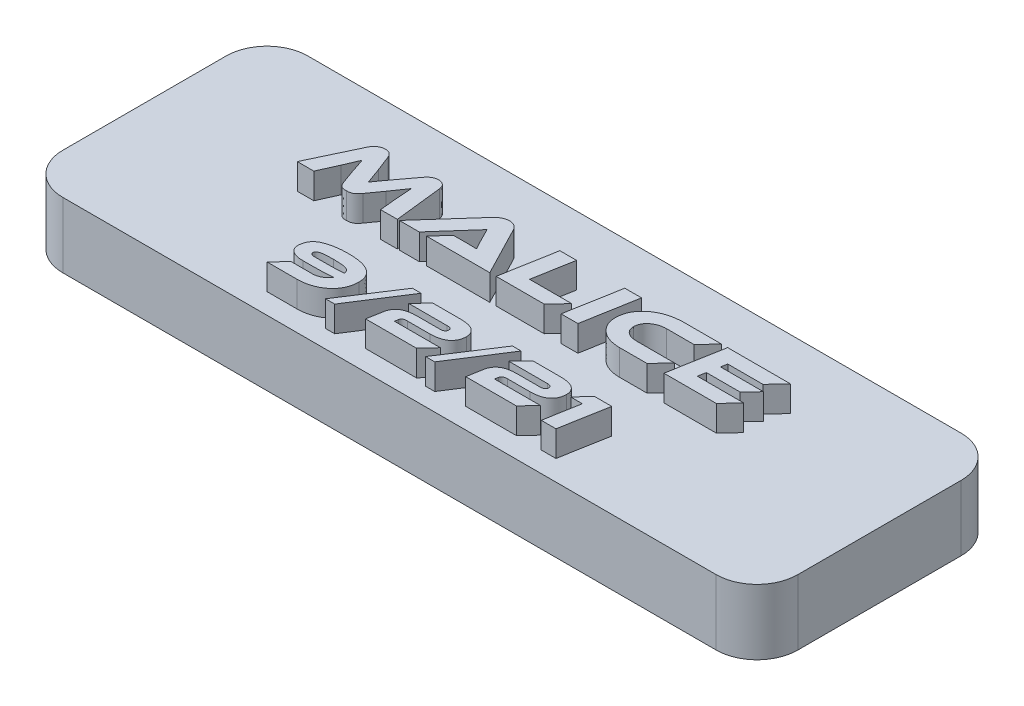
SolidWorks part; units mm, degrees
ref_plane "Front Plane" through (0, 0, 0) normal (0, 0, 1) x (1, 0, 0)
ref_plane "Top Plane" through (0, 0, 0) normal (0, 1, 0) x (1, 0, 0)
ref_plane "Right Plane" through (0, 0, 0) normal (1, 0, 0) x (0, 0, -1)
sketch "Sketch1" plane through (0, 0, 0) normal (0, 1, 0) x (1, 0, 0)
  line L1 (-28.575, 9.525) -> (28.575, 9.525)
  line L2 (-28.575, 9.525) -> (-28.575, -9.525)
  line L3 (-28.575, -9.525) -> (28.575, -9.525)
  line L4 (28.575, 9.525) -> (28.575, -9.525)
  line L5 (-28.575, 9.525) -> (28.575, -9.525) construction
  line L6 (-28.575, -9.525) -> (28.575, 9.525) construction
  point P0 (0, 0)
  dimension "D1" = 57.15
  dimension "D2" = 19.05
extrude "Boss-Extrude1" add sketch "Sketch1" along normal up to surface (5.08 mm away)
fillet "Fillet1" radius 3.175 4 edges at (-28.575, 2.54, 9.525) (-28.575, 2.54, -9.525) (28.575, 2.54, 9.525) (28.575, 2.54, -9.525)
sketch "Sketch3" plane through (0, 5.08, 0) normal (0, 1, 0) x (1, 0, 0)
  line L0 (28.575, -7.9375) -> (-28.575, -7.9375) construction
  line L1 (28.575, -6.35) -> (28.575, 6.35) construction
  line L2 (-28.575, 6.35) -> (-28.575, -6.35) construction
  line L3 (28.575, 0) -> (-28.575, 0) construction
  line L5 (-25.4, -9.525) -> (25.4, -9.525) construction
  line L6 (25.4, 9.525) -> (-25.4, 9.525) construction
  text T0 "Malice\r\n" font "Ethnocentric Rg" height in points 16
  text T1 "9/2/21" font "Ethnocentric Rg" height in points 14
  point P8 (-28.575, 0)
  dimension "D1" = 1.5875
extrude "Boss-Extrude2" add sketch "Sketch3" along normal blind 2
sketch "Sketch4" plane through (0, 0, 0) normal (0, -1, 0) x (1, 0, 0)
  line L0 (25.4, 0) -> (-25.4, 0) construction
  circle A0 centre (-25.4, 0) radius 0.9
  circle A1 centre (25.4, 0) radius 0.9
  point P3 (0, 0)
  dimension "D2" = 1.8
  dimension "D1" = 50.8
extrude "Cut-Extrude1" cut sketch "Sketch4" against normal blind 4
